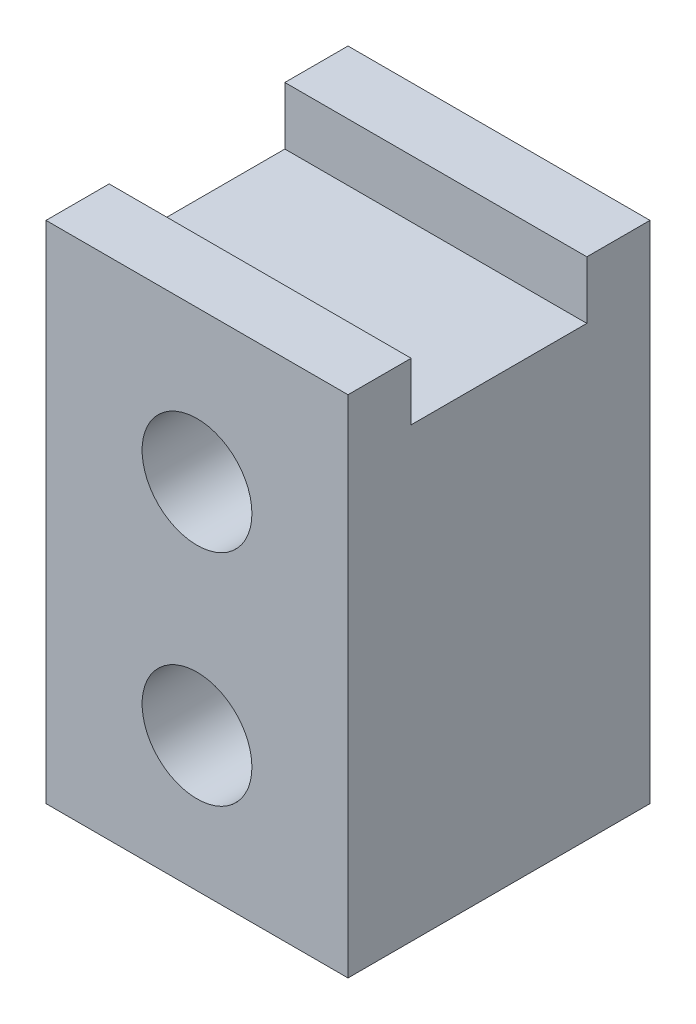
SolidWorks part; units mm, degrees
ref_plane "Alzado" through (0, 0, 0) normal (0, 0, 1) x (1, 0, 0)
ref_plane "Planta" through (0, 0, 0) normal (0, 1, 0) x (1, 0, 0)
ref_plane "Vista lateral" through (0, 0, 0) normal (1, 0, 0) x (0, 0, -1)
sketch "Croquis1" plane through (0, 0, 0) normal (0, 0, 1) x (1, 0, 0)
  line L0 (0, 51.8497) -> (0, -51.8497) construction
  line L2 (-27.5, -46) -> (27.5, -46)
  line L3 (-27.5, -46) -> (-27.5, 46)
  line L4 (-27.5, 46) -> (27.5, 46)
  line L5 (27.5, -46) -> (27.5, 46)
  line L6 (-27.5, -46) -> (27.5, 46) construction
  line L7 (-27.5, 46) -> (27.5, -46) construction
  point P3 (0, 0)
  dimension "D1" = 92
  dimension "D2" = 55
extrude "Saliente-Extruir1" add sketch "Croquis1" along normal blind 55
sketch "Croquis2" plane through (0, 0, 0) normal (0, 0, 1) x (1, 0, 0)
  line L0 (0, 46) -> (0, -46) construction
  line L1 (27.5, 46) -> (-27.5, 46) construction
  line L2 (-27.5, -46) -> (27.5, -46) construction
  circle A0 centre (0, 18.5) radius 10
  circle A1 centre (0, -21.5) radius 10
  dimension "D1" = 20
  dimension "D2" = 20
  dimension "D3" = 40
  dimension "D4" = 27.5
extrude "Cortar-Extruir1" cut sketch "Croquis2" along normal through all
sketch "Croquis3" plane through (-27.5, 0, 0) normal (-1, 0, 0) x (0, 0, 1)
  line L0 (27.5, 46) -> (27.5, -46) construction
  line L1 (55, 46) -> (0, 46) construction
  line L2 (55, -46) -> (0, -46) construction
  line L3 (55, 46) -> (55, -46) construction
  line L4 (11.5, 46) -> (43.5, 46)
  line L5 (11.5, 46) -> (11.5, 35.5)
  line L6 (11.5, 35.5) -> (43.5, 35.5)
  line L7 (43.5, 46) -> (43.5, 35.5)
  dimension "D1" = 10.5
  dimension "D2" = 11.5
  dimension "32" = 32
extrude "Cortar-Extruir2" cut sketch "Croquis3" against normal blind 55
equation "\"10.5.00mm\"=4"
